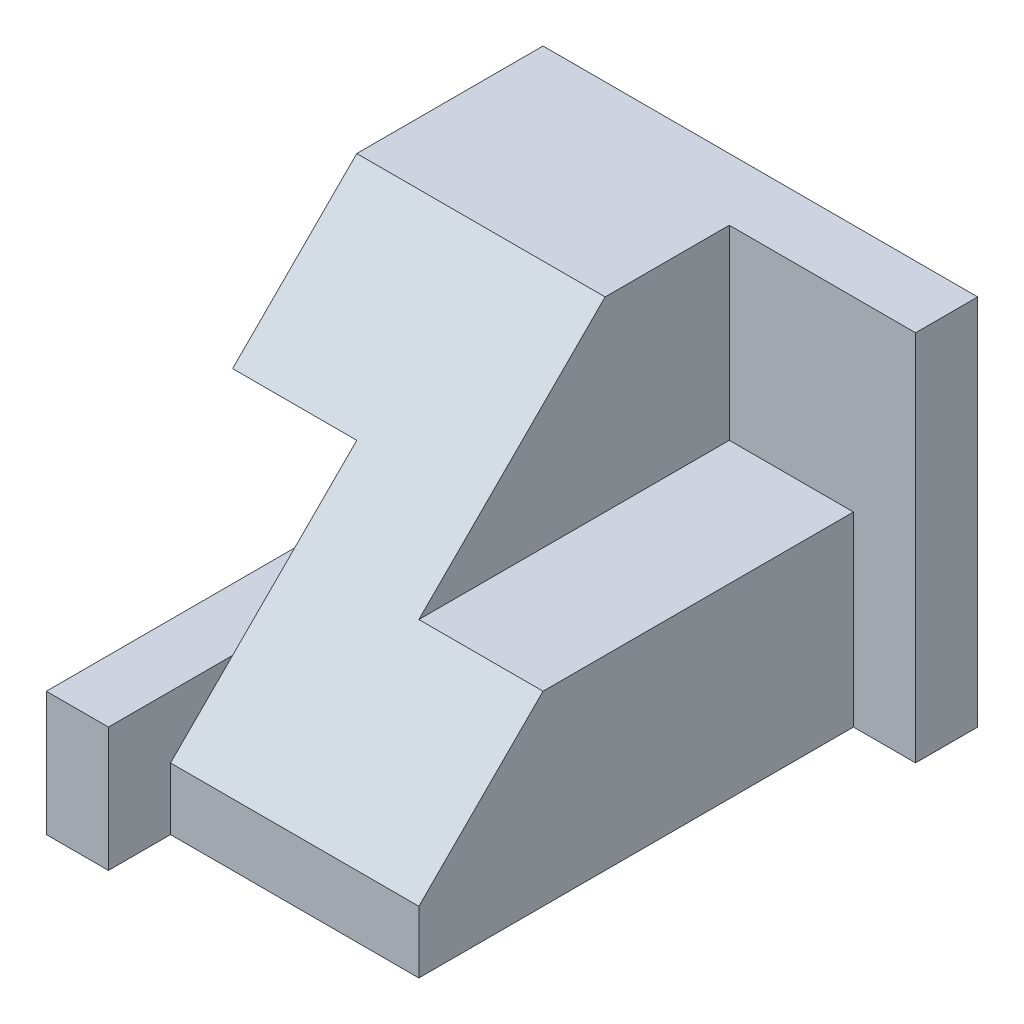
SolidWorks part; units mm, degrees
ref_plane "Front Plane" through (0, 0, 0) normal (0, 0, 1) x (1, 0, 0)
ref_plane "Top Plane" through (0, 0, 0) normal (0, 1, 0) x (1, 0, 0)
ref_plane "Right Plane" through (0, 0, 0) normal (1, 0, 0) x (0, 0, -1)
sketch "Sketch1" plane through (0, 0, 0) normal (0, 0, 1) x (1, 0, 0)
  line L1 (3.5, -3) -> (-3.5, -3)
  line L2 (3.5, -3) -> (3.5, 3)
  line L3 (3.5, 3) -> (-3.5, 3)
  line L4 (-3.5, -3) -> (-3.5, 3)
  line L5 (3.5, -3) -> (-3.5, 3) construction
  line L6 (3.5, 3) -> (-3.5, -3) construction
  point P0 (0, 0)
  dimension "D1" = 7
  dimension "D2" = 6
extrude "Boss-Extrude1" add sketch "Sketch1" along normal blind 9
sketch "Sketch2" plane through (0, 3, 0) normal (0, 1, 0) x (1, 0, 0)
  line L0 (3.5, -1) -> (0.5, -1)
  line L1 (3.5, -9) -> (3.5, 0) construction
  line L2 (0.5, -1) -> (0.5, -6)
  line L3 (0.5, -6) -> (3.5, -6)
  line L4 (3.5, -6) -> (3.5, -1)
  line L5 (3.5, 0) -> (-3.5, 0) construction
  dimension "D1" = 3
  dimension "D2" = 1
  dimension "D3" = 5
extrude "Cut-Extrude1" cut sketch "Sketch2" against normal blind 3
sketch "Sketch3" plane through (0, 3, 0) normal (0, 1, 0) x (1, 0, 0)
  line L0 (3.5, -1) -> (2.5, -1)
  line L1 (3.5, -1) -> (0.5, -1) construction
  line L2 (2.5, -1) -> (2.5, -8)
  line L3 (2.5, -8) -> (-2.5, -8)
  line L4 (-2.5, -8) -> (-2.5, -9)
  line L5 (3.5, -9) -> (-3.5, -9) construction
  line L6 (-2.5, -9) -> (3.5, -9)
  line L7 (3.5, -9) -> (3.5, -1)
  dimension "D1" = 1
  dimension "D2" = 1
  dimension "D3" = 1
extrude "Cut-Extrude2" cut sketch "Sketch3" against normal through all
sketch "Sketch4" plane through (-2.5, 0, 0) normal (1, 0, 0) x (0, 0, -1)
  line L0 (-8, -3) -> (-9, -3)
  line L1 (-9, -3) -> (-9, -1)
  line L2 (-9, -3) -> (-9, 3) construction
  line L3 (-9, -1) -> (-8, -1)
  line L4 (-8, -3) -> (-8, 3) construction
  line L5 (-8, -1) -> (-8, -3)
  dimension "D1" = 2
extrude "Boss-Extrude2" add sketch "Sketch4" along normal blind 1
sketch "Sketch5" plane through (0, 0, 9) normal (0, 0, 1) x (1, 0, 0)
  line L0 (-3.5, 1) -> (-1.5, 1)
  line L1 (-3.5, 3) -> (-3.5, -3) construction
  line L2 (-1.5, 1) -> (-1.5, -1)
  line L3 (-1.5, -1) -> (-2.5, -1)
  line L4 (-2.5, -1) -> (-2.5, -3)
  line L5 (-3.5, -3) -> (-1.5, -3) construction
  line L6 (-2.5, -3) -> (-3.5, -3)
  line L7 (-3.5, -3) -> (-3.5, 1)
  dimension "D1" = 2
extrude "Cut-Extrude3" cut sketch "Sketch5" against normal through all
sketch "Sketch6" plane through (2.5, 0, 0) normal (1, 0, 0) x (0, 0, -1)
  line L0 (-3, 3) -> (-8, -2)
  line L1 (-1, 3) -> (-6, 3) construction
  line L2 (-8, -3) -> (-8, -1) construction
  line L3 (-8, -2) -> (-8, 1)
  line L4 (-8, 1) -> (-9, 1)
  line L5 (-9, 1) -> (-9, 3)
  line L6 (-9, 3) -> (-3, 3)
  dimension "D1" = 1
  dimension "D2" = 3
extrude "Cut-Extrude5" cut sketch "Sketch6" against normal blind 4
ref_plane "Plane1" through (-1.5, 3, 3) normal (0, 0, 1) x (1, 0, 0)
sketch "Sketch8" plane through (-1.5, 0, 0) normal (1, 0, 0) x (0, 0, -1)
  line L0 (-5, 1) -> (-3, 3)
  line L1 (-3, 3) -> (-9, 3)
  line L2 (-9, 3) -> (-9, 1)
  line L3 (-9, 1) -> (-5, 1)
  line L4 (-9, 1) -> (-9, 3) construction
extrude "Cut-Extrude6" cut sketch "Sketch8" against normal through all
